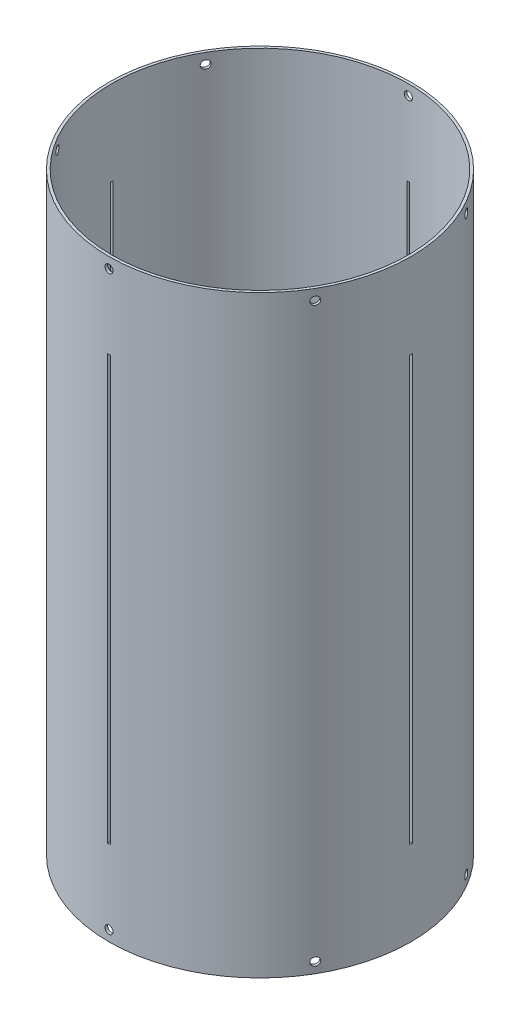
SolidWorks part; units mm, degrees
material "A-Glass Fiber"
ref_plane "Front Plane" through (0, 0, 0) normal (0, 0, 1) x (1, 0, 0)
ref_plane "Top Plane" through (0, 0, 0) normal (0, 1, 0) x (1, 0, 0)
ref_plane "Right Plane" through (0, 0, 0) normal (1, 0, 0) x (0, 0, -1)
sketch "Sketch2" plane through (0, 0, 0) normal (0, 1, 0) x (1, 0, 0)
  circle A0 centre (0, 0) radius 88.9
  circle A1 centre (0, 0) radius 90.4875
  dimension "D1" = 177.8
  dimension "D2" = 1.5875
extrude "Boss-Extrude1" add sketch "Sketch2" along normal blind 355.6
sketch "Sketch3" plane through (0, 0, 0) normal (0, 0, 1) x (1, 0, 0)
  line L0 (0, 0) -> (0, 6.35) construction
  line L1 (-90.4875, 0) -> (90.4875, 0) construction
  line L2 (-90.4875, 0) -> (-90.4875, 355.6) construction
  line L3 (-90.4875, 355.6) -> (90.4875, 355.6) construction
  line L4 (90.4875, 0) -> (90.4875, 355.6) construction
  line L5 (0, 6.35) -> (0, 349.25) construction
  line L7 (0, 355.6) -> (0, 349.25) construction
  circle A0 centre (0, 349.25) radius 2.413
  circle A1 centre (0, 6.35) radius 2.413
  dimension "D2" = 4.826
  dimension "D4" = 4.826
  dimension "D1" = 6.35
  dimension "D3" = 6.35
extrude "Cut-Extrude1" cut sketch "Sketch3" against normal through all both and the other way through all
pattern_circular "CirPattern1" count 6 over 360 about axis through (0, 355.6, 0) along (0, 1, 0) of "Cut-Extrude1"
ref_plane "Plane1" through (-90.4875, 0, 0) normal (-1, 0, 0) x (0, 0, 1)
sketch "Sketch4" plane through (-90.4875, 0, 0) normal (-1, 0, 0) x (0, 0, 1)
  line L0 (0, 0) -> (0, 355.6) construction
  line L2 (-0.7937, 50.8) -> (0.7937, 50.8)
  line L3 (-0.7937, 50.8) -> (-0.7937, 304.8)
  line L4 (-0.7937, 304.8) -> (0.7937, 304.8)
  line L5 (0.7937, 50.8) -> (0.7937, 304.8)
  line L6 (-0.7937, 50.8) -> (0.7937, 304.8) construction
  line L7 (-0.7937, 304.8) -> (0.7937, 50.8) construction
  point P3 (0, 177.8)
  dimension "D1" = 355.6
  dimension "D2" = 1.5875
  dimension "D3" = 254
extrude "Cut-Extrude2" cut sketch "Sketch4" against normal blind 2.54
pattern_circular "CirPattern2" count 4 over 360 about axis through (0, 0, 0) along (0, 1, 0) of "Cut-Extrude2"
